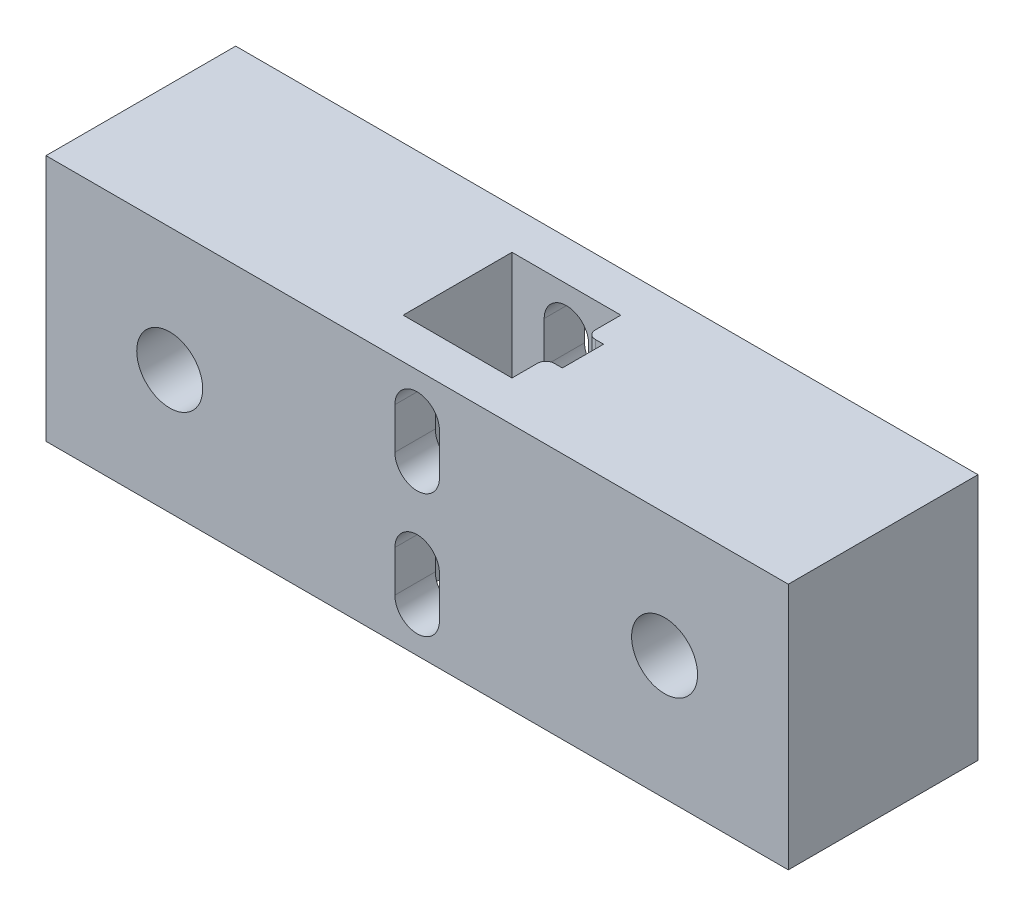
SolidWorks part; units mm, degrees
ref_plane "Plan de face" through (0, 0, 0) normal (0, 0, 1) x (1, 0, 0)
ref_plane "Plan de dessus" through (0, 0, 0) normal (0, 1, 0) x (1, 0, 0)
ref_plane "Plan de droite" through (0, 0, 0) normal (1, 0, 0) x (0, 0, -1)
sketch "Esquisse1" plane through (0, 0, 0) normal (0, 0, 1) x (1, 0, 0)
  line L1 (-4.11, 1.9089) -> (85.89, 1.9089)
  line L2 (-4.11, 1.9089) -> (-4.11, -28.0911)
  line L3 (-4.11, -28.0911) -> (85.89, -28.0911)
  line L4 (85.89, 1.9089) -> (85.89, -28.0911)
  dimension "D1" = 90
  dimension "D2" = 30
extrude "Boss.-Extru.1" add sketch "Esquisse1" along normal blind 23
sketch "Esquisse2" plane through (0, 1.9089, 0) normal (0, 1, 0) x (1, 0, 0)
  line L0 (40.89, -23) -> (40.89, 0) construction
  line L1 (40.89, -11.5) -> (49.49, -11.5) construction
  line L2 (47.49, -4.9) -> (34.29, -4.9)
  line L3 (47.49, -4.9) -> (47.49, -18.1)
  line L4 (85.89, 0) -> (-4.11, 0)
  line L5 (-4.11, 0) -> (-4.11, -23)
  line L6 (-4.11, -23) -> (85.89, -23)
  line L7 (85.89, -23) -> (85.89, 0)
  line L8 (85.89, 0) -> (-4.11, 0)
  line L9 (-4.11, 0) -> (-4.11, -23)
  line L10 (-4.11, -23) -> (85.89, -23)
  line L11 (85.89, -23) -> (85.89, 0)
  line L12 (47.49, -18.1) -> (34.29, -18.1)
  line L13 (34.29, -4.9) -> (34.29, -18.1)
  line L14 (47.49, -4.9) -> (34.29, -18.1) construction
  line L15 (47.49, -18.1) -> (34.29, -4.9) construction
  line L16 (47.49, -14) -> (49.49, -14)
  line L17 (47.49, -14) -> (47.49, -9)
  line L18 (47.49, -9) -> (49.49, -9)
  line L19 (49.49, -14) -> (49.49, -9)
  point P6 (40.89, -11.5)
  point P7 (40.89, -11.5)
  dimension "D2" = 13.2
  dimension "D3" = 13.2
  dimension "D4" = 2
  dimension "D5" = 5
  dimension "D1" = 0
extrude "Enlèv. mat.-Extru.1" cut sketch "Esquisse2" against normal through all contours L2 L13 L12 L3 | L16 L19 L18 L3
sketch "Esquisse3" plane through (0, 0, 0) normal (0, 0, -1) x (-1, 0, 0)
  line L0 (-40.89, -28.0911) -> (-40.89, 1.9089) construction
  line L1 (4.11, -13.0911) -> (-85.89, -13.0911) construction
  line L4 (4.11, -28.0911) -> (4.11, 1.9089)
  line L5 (4.11, 1.9089) -> (-85.89, 1.9089)
  line L6 (-85.89, 1.9089) -> (-85.89, -28.0911)
  line L7 (-85.89, -28.0911) -> (4.11, -28.0911)
  line L8 (4.11, -28.0911) -> (4.11, 1.9089)
  line L9 (4.11, 1.9089) -> (-85.89, 1.9089)
  line L10 (-85.89, 1.9089) -> (-85.89, -28.0911)
  line L11 (-85.89, -28.0911) -> (4.11, -28.0911)
  circle A0 centre (-10.89, -13.0911) radius 4
  circle A1 centre (-70.89, -13.0911) radius 4
  point P8 (-10.89, -13.0911)
  dimension "D3" = 8
  dimension "D2" = 15
  dimension "D1" = 0
sketch "Esquisse4" plane through (0, 0, 0) normal (0, 0, -1) x (-1, 0, 0)
  line L0 (-40.89, -28.0911) -> (-40.89, 1.9089) construction
  line L1 (-40.89, -23.0911) -> (-40.89, -18.0911) construction
  line L2 (-43.59, -23.0911) -> (-43.59, -18.0911)
  line L3 (-38.19, -23.0911) -> (-38.19, -18.0911)
  line L4 (4.11, -28.0911) -> (4.11, 1.9089)
  line L5 (4.11, 1.9089) -> (-85.89, 1.9089)
  line L6 (-85.89, 1.9089) -> (-85.89, -28.0911)
  line L7 (-85.89, -28.0911) -> (4.11, -28.0911)
  line L8 (4.11, -28.0911) -> (4.11, 1.9089)
  line L9 (4.11, 1.9089) -> (-85.89, 1.9089)
  line L10 (-85.89, 1.9089) -> (-85.89, -28.0911)
  line L11 (-85.89, -28.0911) -> (4.11, -28.0911)
  line L12 (-34.29, 1.9089) -> (-47.49, 1.9089)
  line L13 (-47.49, 1.9089) -> (-47.49, -28.0911)
  line L14 (-47.49, -28.0911) -> (-34.29, -28.0911)
  line L15 (-34.29, -28.0911) -> (-34.29, 1.9089)
  line L16 (-34.29, 1.9089) -> (-47.49, 1.9089)
  line L17 (-47.49, 1.9089) -> (-47.49, -28.0911)
  line L18 (-47.49, -28.0911) -> (-34.29, -28.0911)
  line L19 (-34.29, -28.0911) -> (-34.29, 1.9089)
  line L20 (-47.49, -13.0911) -> (-34.29, -13.0911) construction
  line L21 (-40.89, -3.0911) -> (-40.89, -8.0911) construction
  line L22 (-43.59, -3.0911) -> (-43.59, -8.0911)
  line L23 (-38.19, -3.0911) -> (-38.19, -8.0911)
  arc A2 (-43.59, -23.0911) -> (-38.19, -23.0911) centre (-40.89, -23.0911) ccw
  arc A3 (-38.19, -18.0911) -> (-43.59, -18.0911) centre (-40.89, -18.0911) ccw
  arc A4 (-43.59, -3.0911) -> (-38.19, -3.0911) centre (-40.89, -3.0911) cw
  arc A5 (-38.19, -8.0911) -> (-43.59, -8.0911) centre (-40.89, -8.0911) cw
  point P12 (-40.89, -20.5911)
  point P21 (-40.89, -5.5911)
  dimension "D3" = 2.7
  dimension "D4" = 5
  dimension "D5" = 5
  dimension "D1" = 0
  dimension "D2" = 0
extrude "Enlèv. mat.-Extru.2" cut sketch "Esquisse3" against normal through all contours A0 | A1
extrude "Enlèv. mat.-Extru.3" cut sketch "Esquisse4" against normal through all contours A5 L23 A4 L22 | L2 A3 L3 A2
fillet "Congé1" radius 1 2 edges at (47.49, -13.0911, 9) (47.49, -13.0911, 14)
